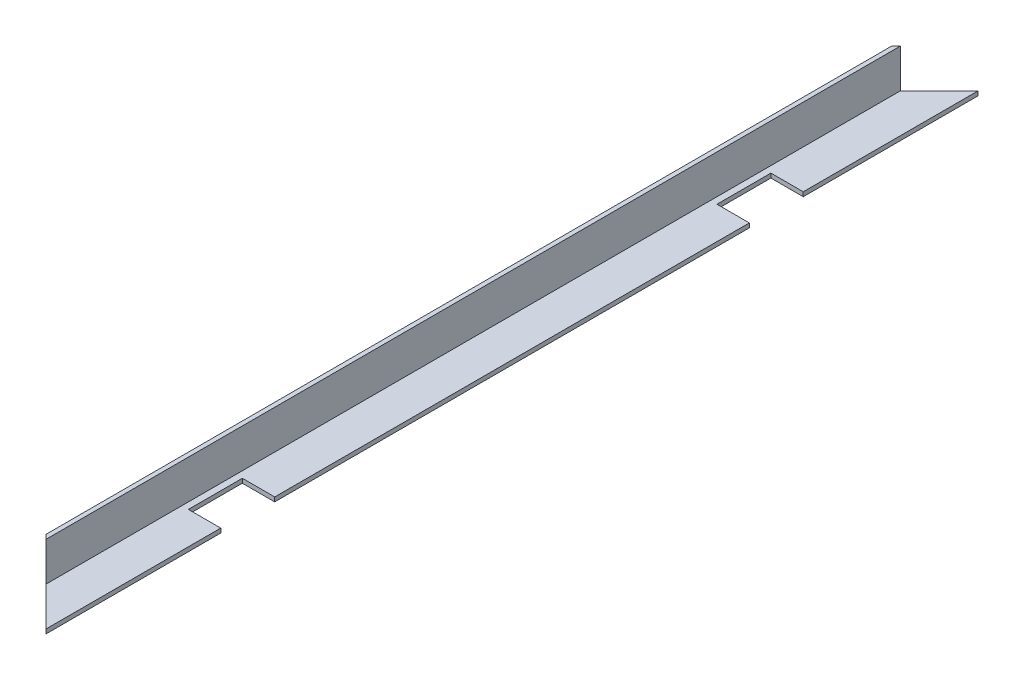
SolidWorks part; units mm, degrees
ref_plane "Front Plane" through (0, 0, 0) normal (0, 0, 1) x (1, 0, 0)
ref_plane "Top Plane" through (0, 0, 0) normal (0, 1, 0) x (1, 0, 0)
ref_plane "Right Plane" through (0, 0, 0) normal (1, 0, 0) x (0, 0, -1)
sketch "Sketch1" plane through (0, 0, 0) normal (0, 0, 1) x (1, 0, 0)
  line L0 (0, 0) -> (20, 0)
  line L4 (2, 20) -> (0, 20)
  line L5 (0, 20) -> (0, 0)
  line L6 (2, 20) -> (2, 2)
  line L7 (2, 2) -> (20, 2)
  line L8 (20, 2) -> (20, 0)
  dimension "D1" = 20
  dimension "D2" = 20
  dimension "D3" = 2
  dimension "D4" = 2
extrude "Boss-Extrude1" add sketch "Sketch1" along normal blind 432
sketch "Sketch2" plane through (0, 2, 0) normal (0, 1, 0) x (1, 0, 0)
  line L0 (0, -432) -> (20, -432)
  line L1 (20, -432) -> (0, -412)
  line L2 (0, -432) -> (0, 0) construction
  line L3 (0, -412) -> (0, -432)
  line L4 (20, 0) -> (0, -20)
  line L5 (0, -20) -> (0, 0)
  line L6 (0, 0) -> (20, 0)
  dimension "D1" = 20
extrude "Cut-Extrude1" cut sketch "Sketch2" along normal mid plane 46
sketch "Sketch3" plane through (0, 2, 0) normal (0, 1, 0) x (1, 0, 0)
  line L0 (20, -432) -> (20, 0) construction
  line L1 (20, -81) -> (5, -81)
  line L2 (20, -81) -> (20, -106)
  line L3 (20, -106) -> (5, -106)
  line L4 (5, -81) -> (5, -106)
  line L5 (-68.477, -216) -> (103.9889, -216) construction
  line L6 (20, -326) -> (5, -326)
  line L7 (5, -351) -> (5, -326)
  line L8 (20, -351) -> (5, -351)
  line L9 (20, -351) -> (20, -326)
  dimension "D1" = 15
  dimension "D2" = 81
  dimension "D3" = 25
  dimension "D4" = 81
extrude "Cut-Extrude2" cut sketch "Sketch3" against normal through all
